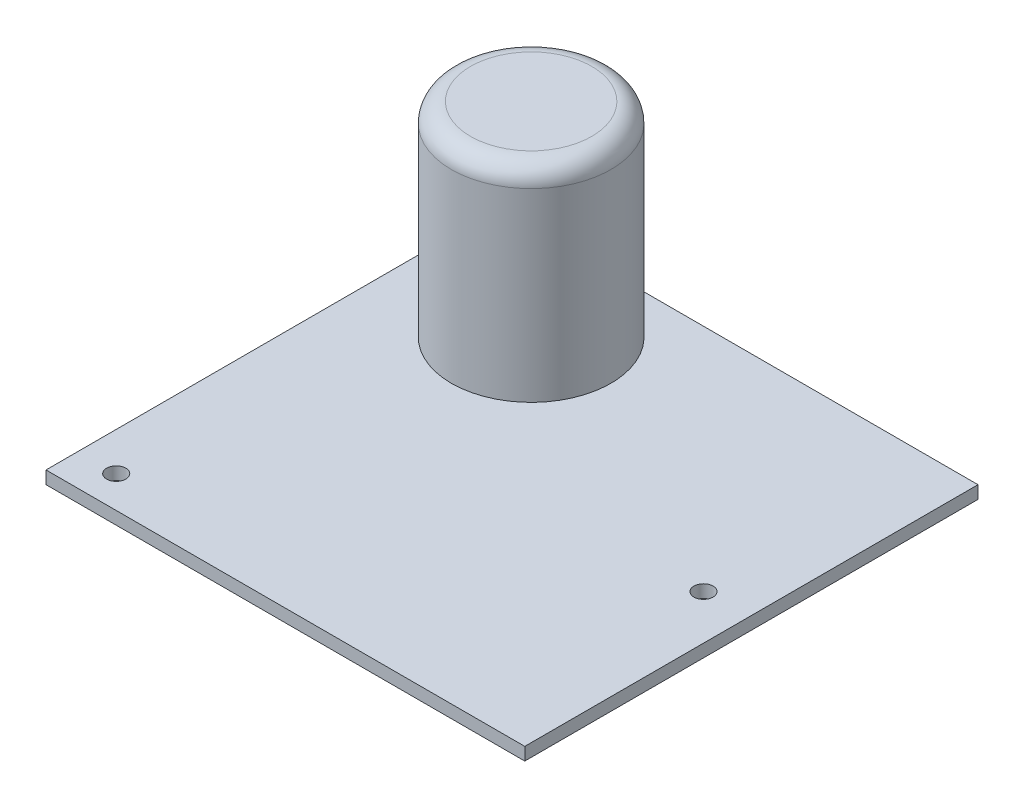
SolidWorks part; units mm, degrees
ref_plane "Plan de face" through (0, 0, 0) normal (0, 0, 1) x (1, 0, 0)
ref_plane "Plan de dessus" through (0, 0, 0) normal (0, 1, 0) x (1, 0, 0)
ref_plane "Plan de droite" through (0, 0, 0) normal (1, 0, 0) x (0, 0, -1)
sketch "Esquisse1" plane through (0, 0, 0) normal (0, 1, 0) x (1, 0, 0)
  line L1 (-37.5, 35) -> (37.5, 35)
  line L2 (-37.5, 35) -> (-37.5, -36)
  line L3 (-37.5, -36) -> (37.5, -36)
  line L4 (37.5, 35) -> (37.5, -36)
  circle A0 centre (-31.5, 30) radius 1.5
  circle A1 centre (-31.5, -31) radius 1.5
  circle A2 centre (30.5, -1) radius 1.5
  dimension "D5" = 3
  dimension "D7" = 3
  dimension "D8" = 3
  dimension "D1" = 75
  dimension "D2" = 71
  dimension "D3" = 35
  dimension "D4" = 37.5
  dimension "D9" = 5
  dimension "D10" = 6
  dimension "D11" = 5
  dimension "D12" = 6
  dimension "D15" = 7
  dimension "D16" = 35
extrude "Boss.-Extru.1" add sketch "Esquisse1" along normal blind 2
sketch "Esquisse3" plane through (0, 2, 0) normal (0, 1, 0) x (1, 0, 0)
  line L0 (37.5, 35) -> (-37.5, 35) construction
  line L1 (-37.5, 35) -> (-37.5, -36) construction
  circle A0 centre (-17.5, 20) radius 12.5
  dimension "D1" = 25
  dimension "D2" = 15
  dimension "D3" = 20
extrude "Boss.-Extru.2" add sketch "Esquisse3" along normal blind 32
fillet "Congé1" radius 3 1 edges at (-17.5, 34, -7.5)
